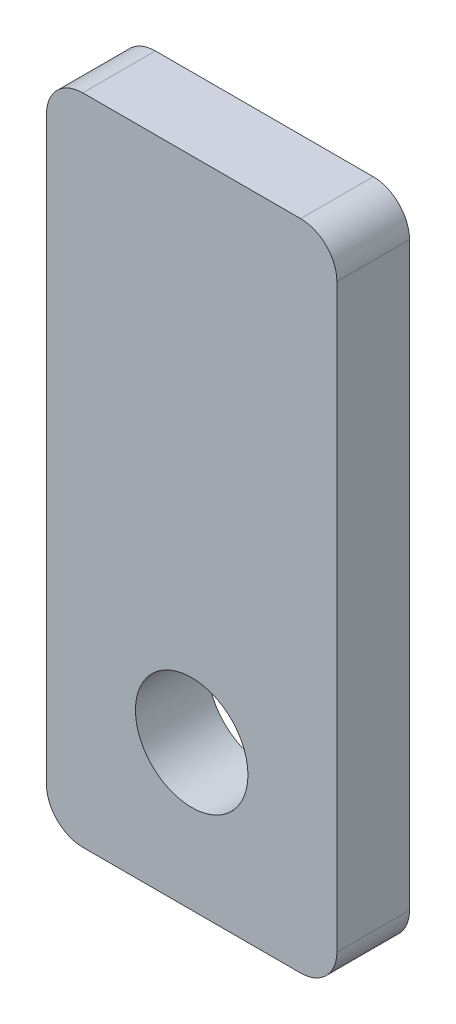
SolidWorks part; units mm, degrees
material "Thornel Mat VMA"
ref_plane "前视基准面" through (0, 0, 0) normal (0, 0, 1) x (1, 0, 0)
ref_plane "上视基准面" through (0, 0, 0) normal (0, 1, 0) x (1, 0, 0)
ref_plane "右视基准面" through (0, 0, 0) normal (1, 0, 0) x (0, 0, -1)
sketch "草图1" plane through (0, 0, 0) normal (0, 0, 1) x (1, 0, 0)
  line L1 (-3, 9) -> (3, 9)
  line L2 (-4, 8) -> (-4, -8)
  line L3 (-3, -9) -> (3, -9)
  line L4 (4, 8) -> (4, -8)
  line L5 (-4, 9) -> (4, -9) construction
  line L6 (-4, -9) -> (4, 9) construction
  circle A0 centre (0, -5) radius 1.55
  arc A1 (-4, -8) -> (-3, -9) centre (-3, -8) ccw
  arc A2 (3, -9) -> (4, -8) centre (3, -8) ccw
  arc A3 (4, 8) -> (3, 9) centre (3, 8) ccw
  arc A4 (-3, 9) -> (-4, 8) centre (-3, 8) ccw
  point P0 (0, 0)
  dimension "D3" = 4
  dimension "D4" = 1
  dimension "D1" = 8
  dimension "D2" = 18
extrude "凸台-拉伸1" add sketch "草图1" along normal blind 2
